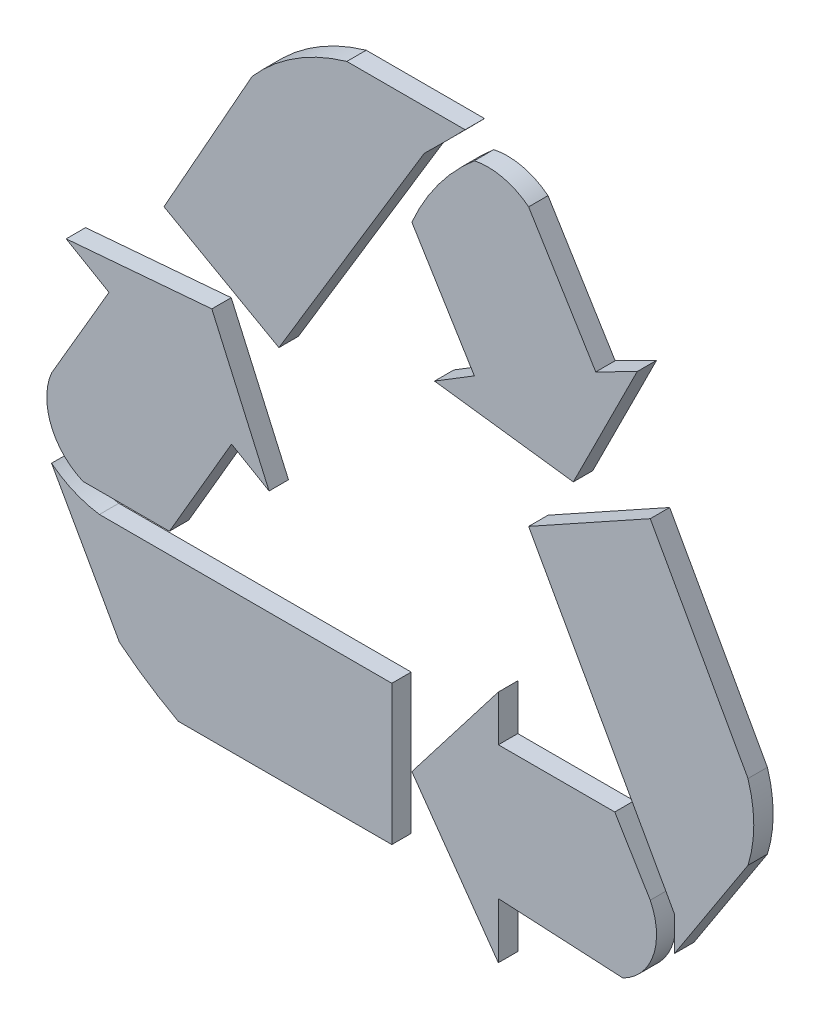
SolidWorks part; units mm, degrees
ref_plane "Front Plane" through (0, 0, 0) normal (0, 0, 1) x (1, 0, 0)
ref_plane "Top Plane" through (0, 0, 0) normal (0, 1, 0) x (1, 0, 0)
ref_plane "Right Plane" through (0, 0, 0) normal (1, 0, 0) x (0, 0, -1)
sketch "Sketch1" plane through (0, 0, 0) normal (0, 0, 1) x (1, 0, 0)
  line L0 (36, 116.5) -> (180, 116.5) construction
  line L1 (5.637, 11.9438) -> (7.186, 11.9438)
  line L2 (3.2431, 9.0993) -> (4.3978, 11.1552)
  line L3 (3.2431, 9.0993) -> (4.748, 8.2541)
  line L5 (6.6509, 11.4087) -> (4.748, 8.2541)
  line L6 (6.4887, 10.5469) -> (7.3071, 9.2133)
  line L7 (7.3071, 9.2133) -> (6.7855, 8.8932)
  line L8 (6.7855, 8.8932) -> (8.6031, 8.6587)
  line L9 (8.6031, 8.6587) -> (9.4391, 10.3283)
  line L10 (9.4391, 10.3283) -> (8.8967, 10.0526)
  line L11 (8.8967, 10.0526) -> (8.0176, 11.4851)
  line L13 (8.0176, 7.8617) -> (9.61, 8.7454)
  line L14 (9.61, 8.7454) -> (10.8898, 6.4391)
  line L15 (8.0176, 7.8617) -> (9.9277, 4.4195)
  line L16 (9.9277, 4.4195) -> (9.9277, 3.9733)
  line L17 (9.9277, 3.9733) -> (10.8898, 5.4546)
  line L18 (7.6215, 5.1871) -> (9.1451, 5.1871)
  line L19 (9.1451, 5.1871) -> (9.61, 4.4195)
  line L20 (7.6215, 5.1871) -> (7.6215, 5.7858)
  line L21 (7.6215, 5.7858) -> (6.4887, 4.3165)
  line L22 (6.4887, 4.3165) -> (7.6215, 2.7156)
  line L23 (7.6215, 2.7156) -> (7.6215, 3.4432)
  line L24 (7.6215, 3.4432) -> (9.2517, 3.3577)
  line L25 (1.9625, 8.095) -> (3.8695, 8.2541)
  line L26 (3.8695, 8.2541) -> (4.6195, 6.564)
  line L27 (4.6195, 6.564) -> (4.1282, 6.8505)
  line L28 (4.1282, 6.8505) -> (3.3142, 5.4546)
  line L29 (3.3142, 5.4546) -> (2.1828, 5.4546)
  line L30 (1.9625, 8.095) -> (2.5232, 7.768)
  line L31 (2.5232, 7.768) -> (1.771, 6.4781)
  line L32 (6.2262, 5.1871) -> (6.2262, 3.3577)
  line L33 (6.2262, 3.3577) -> (3.4308, 3.3577)
  line L34 (1.771, 5.4546) -> (2.6602, 3.8685)
  line L35 (2.3981, 5.1871) -> (6.2262, 5.1871)
  arc A0 (4.3978, 11.1552) -> (5.637, 11.9438) centre (6.3605, 9.439) cw
  arc A1 (7.3071, 11.6524) -> (8.0176, 11.4851) centre (7.4845, 10.8131) cw
  arc A2 (10.8898, 6.4391) -> (10.8898, 5.4546) centre (9.3295, 5.9469) cw
  arc A3 (9.61, 4.4195) -> (9.2517, 3.3577) centre (8.9, 4.0678) cw
  arc A4 (2.1828, 5.4546) -> (1.771, 6.4781) centre (2.4886, 6.1723) cw
  arc A5 (3.4308, 3.3577) -> (2.6602, 3.8685) centre (5.7755, 7.7323) cw
  arc A6 (2.3981, 5.1871) -> (1.771, 5.4546) centre (2.5802, 6.4829) cw
  arc A7 (6.6509, 11.4087) -> (7.186, 11.9438) centre (-17.7825, 36.3772) ccw
  arc A8 (6.4887, 10.5469) -> (7.3071, 11.6524) centre (9.2845, 9.333) cw
  point P53 (0, 0)
extrude "Boss-Extrude1" add sketch "Sketch1" along normal blind 0.254
